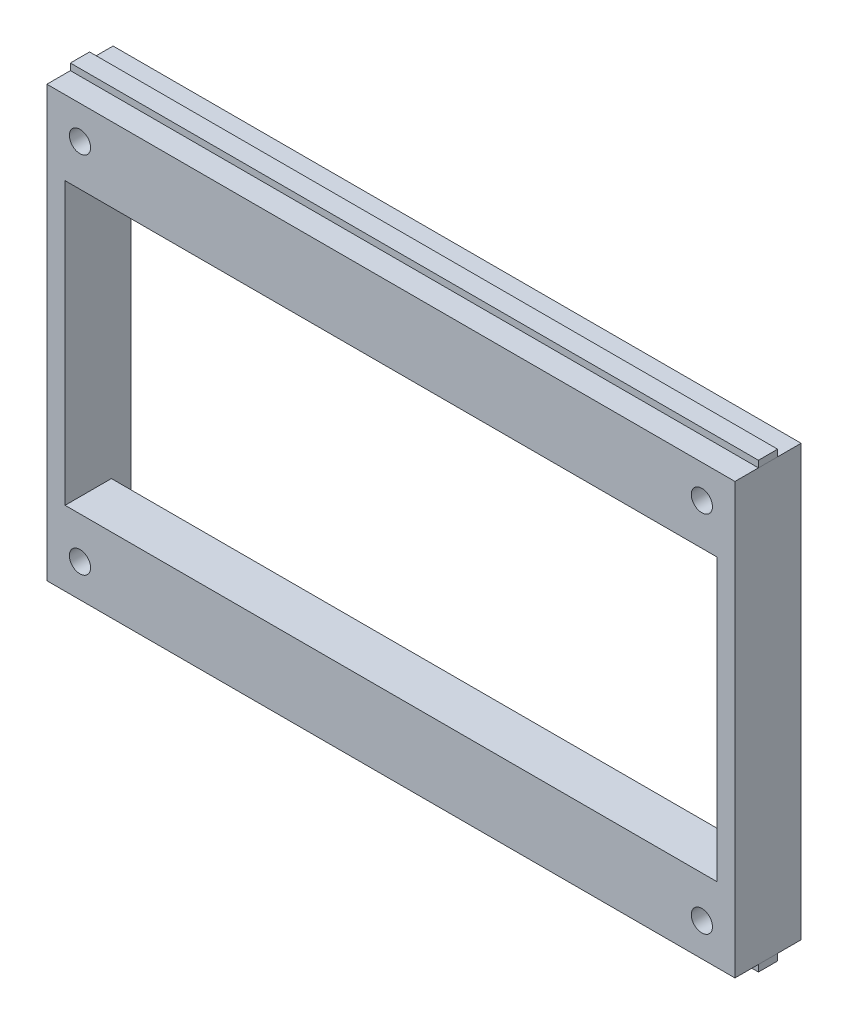
SolidWorks part; units mm, degrees
ref_plane "Front Plane" through (0, 0, 0) normal (0, 0, 1) x (1, 0, 0)
ref_plane "Top Plane" through (0, 0, 0) normal (0, 1, 0) x (1, 0, 0)
ref_plane "Right Plane" through (0, 0, 0) normal (1, 0, 0) x (0, 0, -1)
sketch "Main Sketch" plane through (0, 0, 0) normal (0, 0, 1) x (1, 0, 0)
  line L1 (-52, 32.5) -> (52, 32.5)
  line L2 (-52, 32.5) -> (-52, -32.5)
  line L3 (-52, -32.5) -> (52, -32.5)
  line L4 (52, 32.5) -> (52, -32.5)
  point P4 (-52, 0)
  point P6 (0, 32.5)
  dimension "D1" = 104
  dimension "D2" = 65
extrude "Main Extrusion" add sketch "Main Sketch" along normal blind 10
sketch "Esquisse2" plane through (-52, 0, 0) normal (-1, 0, 0) x (0, 0, 1)
  line L0 (10, 32.5) -> (0, 32.5) construction
  line L1 (6.45, 33.5) -> (3.55, 33.5)
  line L2 (6.45, 33.5) -> (6.45, 32.5)
  line L3 (6.45, 32.5) -> (3.55, 32.5)
  line L4 (3.55, 33.5) -> (3.55, 32.5)
  line L5 (10, -32.5) -> (0, -32.5) construction
  line L6 (3.55, -32.5) -> (6.45, -32.5)
  line L7 (3.55, -32.5) -> (3.55, -33.5)
  line L8 (3.55, -33.5) -> (6.45, -33.5)
  line L9 (6.45, -32.5) -> (6.45, -33.5)
  point P12 (4.1062, -33.5)
  point P13 (6.3867, -33.5)
  point P14 (5, 32.5)
  point P15 (5, 32.5)
  point P16 (-6.1439, -33.5)
  dimension "D1" = 2.9
  dimension "D2" = 1
extrude "MakerBeam Attachment" add sketch "Esquisse2" against normal up to surface (104 mm away) separate body up to face at (52, 0, 5)
sketch "Esquisse3" plane through (0, 0, 10) normal (0, 0, 1) x (1, 0, 0)
  line L0 (52, -32.5) -> (-52, -32.5) construction
  line L1 (-49.25, 21.25) -> (49.25, 21.25)
  line L2 (-49.25, 21.25) -> (-49.25, -21.25)
  line L3 (-49.25, -21.25) -> (49.25, -21.25)
  line L4 (49.25, 21.25) -> (49.25, -21.25)
  line L5 (-52, 32.5) -> (-52, -32.5) construction
  point P4 (0, -21.25)
  point P7 (0, -32.5)
  point P8 (-52, 0)
  point P11 (-49.25, 0)
  dimension "D1" = 98.5
  dimension "D2" = 42.5
extrude "Hole LCD Screen" cut sketch "Esquisse3" against normal through all
sketch "Esquisse4" plane through (0, 0, 10) normal (0, 0, 1) x (1, 0, 0)
  line L0 (52, 32.5) -> (-52, 32.5) construction
  line L1 (52, -32.5) -> (-52, -32.5) construction
  line L2 (-52, 32.5) -> (-52, -32.5) construction
  line L3 (52, -32.5) -> (52, 32.5) construction
  circle A0 centre (-47, 27.5) radius 1.6
  circle A1 centre (47, 27.5) radius 1.6
  circle A2 centre (-47, -27.5) radius 1.6
  circle A3 centre (47, -27.5) radius 1.6
  dimension "D1" = 3.2
  dimension "D2" = 5
  dimension "D3" = 5
  dimension "D4" = 5
  dimension "D5" = 5
  dimension "D6" = 55
  dimension "D7" = 94
extrude "Holes Support LCD" cut sketch "Esquisse4" against normal through all
sketch "Esquisse5" plane through (0, 0, 0) normal (0, 0, -1) x (-1, 0, 0)
  line L1 (-49.25, 30) -> (49.25, 30)
  line L2 (-49.25, 30) -> (-49.25, -30)
  line L3 (-49.25, -30) -> (49.25, -30)
  line L4 (49.25, 30) -> (49.25, -30)
  line L6 (-52, 32.5) -> (52, 32.5) construction
  line L7 (52, -32.5) -> (-52, -32.5) construction
  line L8 (-49.25, -21.25) -> (-49.25, 21.25) construction
  line L9 (49.25, 21.25) -> (49.25, -21.25) construction
  dimension "D1" = 2.5
  dimension "D2" = 2.5
extrude "SupportTopAndBottom" cut sketch "Esquisse5" against normal blind 3
sketch "Esquisse6" plane through (0, 0, 3) normal (0, 0, -1) x (-1, 0, 0)
  line L0 (49.25, 30) -> (-49.25, 30) construction
  line L1 (-44, 25) -> (44, 25)
  line L2 (-44, 25) -> (-44, 30)
  line L3 (-44, 30) -> (44, 30)
  line L4 (44, 25) -> (44, 30)
  line L5 (-52, 30) -> (-52, -30) construction
  line L6 (52, -30) -> (52, 30) construction
  line L7 (-49.25, -30) -> (49.25, -30) construction
  line L8 (-44, -30) -> (44, -30)
  line L9 (-44, -30) -> (-44, -25)
  line L10 (-44, -25) -> (44, -25)
  line L11 (44, -30) -> (44, -25)
  dimension "D1" = 8
  dimension "D2" = 8
  dimension "D3" = 5
extrude "Holes For Pins" cut sketch "Esquisse6" against normal blind 3
